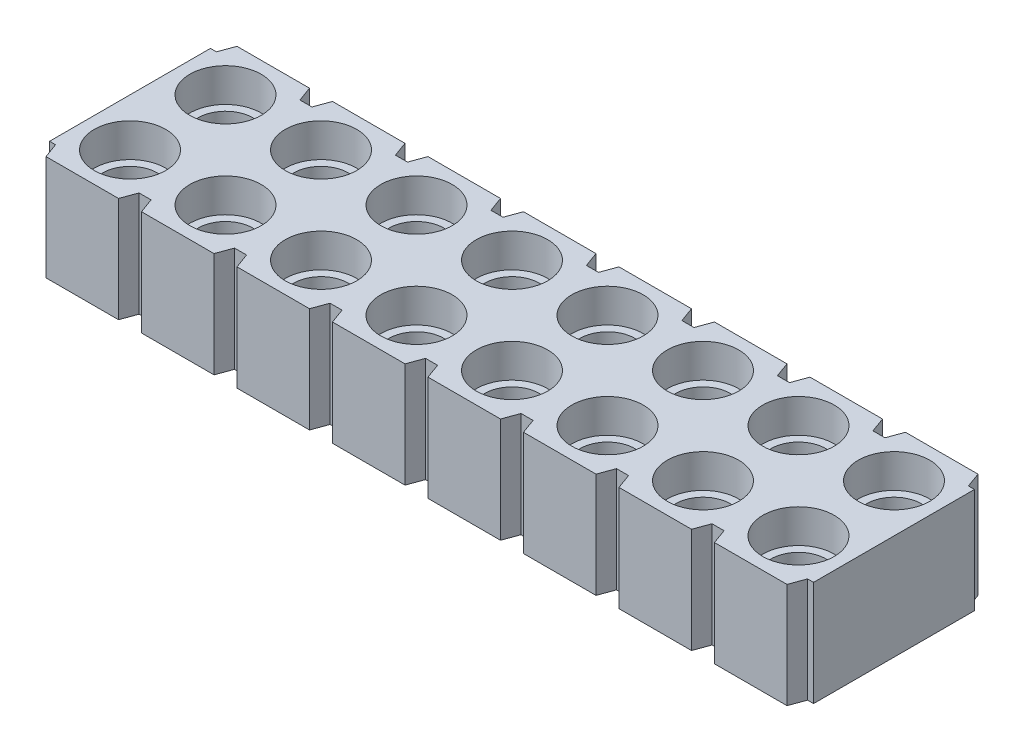
SolidWorks part; units mm, degrees
material "PCT Polyester"
ref_plane "Front Plane" through (0, 0, 0) normal (0, 0, 1) x (1, 0, 0)
ref_plane "Top Plane" through (0, 0, 0) normal (0, 1, 0) x (1, 0, 0)
ref_plane "Right Plane" through (0, 0, 0) normal (1, 0, 0) x (0, 0, -1)
sketch "Sketch1" plane through (0, 0, 0) normal (0, 1, 0) x (1, 0, 0)
  line L0 (20.0144, 0.4) -> (19.8544, 0.4)
  line L1 (20.0144, 4.6799) -> (20.0144, 0.4)
  line L2 (-0.3056, 4.6799) -> (-0.1456, 4.6799)
  line L3 (-0.3056, 4.6799) -> (-0.3056, 0.4)
  line L4 (0, 0) -> (19.7087, 0)
  line L5 (0, 5.08) -> (-0.1456, 4.6799)
  line L6 (0, 0) -> (-0.1456, 0.4)
  line L7 (-0.3056, 0.4) -> (-0.1456, 0.4)
  line L9 (19.7087, 0) -> (19.8544, 0.4)
  line L10 (19.7087, 5.08) -> (19.8544, 4.6799)
  line L11 (20.0144, 4.6799) -> (19.8544, 4.6799)
  line L16 (19.7087, 5.08) -> (0, 5.08)
  dimension "D2" = 5.08
  dimension "D3" = 20
  dimension "D4" = 0.4
  dimension "D5" = 0.4
  dimension "D7" = 0.16
  dimension "INSLENGTH" = 20.32
extrude "Extrude1" add sketch "Sketch1" against normal blind 2.794
hole_wizard "Hole1" positions "3DSketch2" profile "Sketch3" legacy end condition through all
sketch3d "3DSketch2"
  line L4 (0, 0, 0) -> (19.7087, 0, 0) construction
  line L5 (-0.3056, 0, -4.6799) -> (-0.3056, 0, -0.4) construction
  point P0 (0.9644, 0, -1.27)
  dimension "D1" = 1.27
  dimension "D2" = 1.27
sketch "Sketch3" plane through (0.9644, 0, -1.27) normal (1, 0, 0) x (0, 0, 1)
  line L0 (0, 0) -> (0, 2.794)
  line L1 (0, 2.794) -> (0.73, 2.794)
  line L2 (0.73, 2.794) -> (0.73, 0.8941)
  line L3 (0.73, 0.8941) -> (0.95, 0.8941)
  line L4 (0.95, 0.8941) -> (0.95, 0)
  line L5 (0.95, 0) -> (0, 0)
  line L6 (0, 110) -> (0, -10) construction
  dimension "Diameter" = 1.46
  dimension "Depth" = 2.794
  dimension "C-Bore Diameter" = 1.8999
  dimension "C-Bore Depth" = 0.8941
sketch "Sketch4" plane through (0, 0, 0) normal (0, 1, 0) x (1, 0, 0)
  line L0 (1.9288, 0) -> (2.54, 0)
  line L2 (0, 0) -> (19.7087, 0) construction
  line L5 (2.0744, 0.4) -> (1.9288, 0)
  line L6 (2.3944, 0.4) -> (2.54, 0)
  line L7 (19.7087, 5.08) -> (0, 5.08) construction
  line L8 (2.0744, 0.4) -> (2.3944, 0.4)
  line L10 (2.0744, 4.6799) -> (2.3944, 4.6799)
  line L11 (2.3944, 4.6799) -> (2.54, 5.08)
  line L12 (2.0744, 4.6799) -> (1.9288, 5.08)
  line L13 (1.9288, 5.08) -> (2.54, 5.08)
  line L17 (-0.3056, 4.6799) -> (-0.3056, 0.4) construction
  dimension "D1" = 0.4
  dimension "D2" = 0.32
  dimension "D3" = 70
  dimension "D4" = 0.6112
  dimension "D5" = 0.4001
  dimension "D6" = 2.2344
extrude "Extrude2" cut sketch "Sketch4" against normal blind 2.794
pattern_linear "Hole Pattern" count 32 spacing 2.54 along (1, 0, 0) count 2 spacing 2.54 along (0, 0, -1) of "Hole1"
pattern_linear "Slot Pattern" count 31 spacing 2.54 along (1, 0, 0) of "Extrude2"
